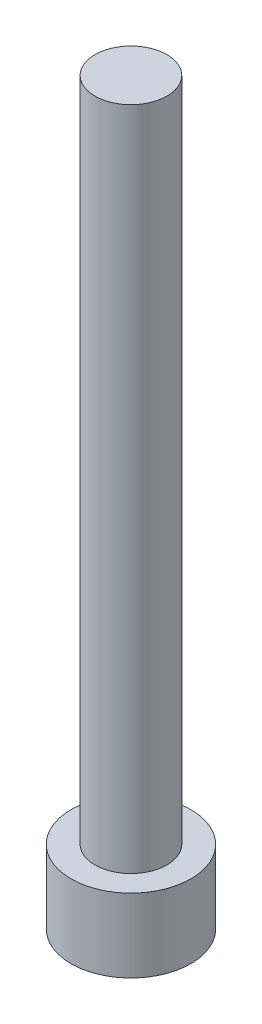
SolidWorks part; units mm, degrees
ref_plane "Front Plane" through (0, 0, 0) normal (0, 0, 1) x (1, 0, 0)
ref_plane "Top Plane" through (0, 0, 0) normal (0, 1, 0) x (1, 0, 0)
ref_plane "Right Plane" through (0, 0, 0) normal (1, 0, 0) x (0, 0, -1)
sketch "Sketch1" plane through (0, 0, 0) normal (0, 1, 0) x (1, 0, 0)
  circle A0 centre (0, 0) radius 2.8575
  dimension "D1" = 5.715
extrude "Boss-Extrude1" add sketch "Sketch1" along normal blind 3.5052
sketch "Sketch2" plane through (0, 0, 0) normal (0, -1, 0) x (1, 0, 0)
  line L1 (1.604, 0) -> (0.802, 1.3891)
  line L2 (0.802, 1.3891) -> (-0.802, 1.3891)
  line L3 (-0.802, 1.3891) -> (-1.604, 0)
  line L4 (-1.604, 0) -> (-0.802, -1.3891)
  line L5 (-0.802, -1.3891) -> (0.802, -1.3891)
  line L6 (0.802, -1.3891) -> (1.604, 0)
  circle A0 centre (0, 0) radius 1.3891 construction
  dimension "D1" = 2.7781
extrude "Cut-Extrude1" cut sketch "Sketch2" against normal blind 1.9558
sketch "Sketch3" plane through (0, 3.5052, 0) normal (0, 1, 0) x (1, 0, 0)
  circle A0 centre (0, 0) radius 1.7145
  dimension "D1" = 3.429
extrude "Boss-Extrude2" add sketch "Sketch3" along normal blind 31.75
